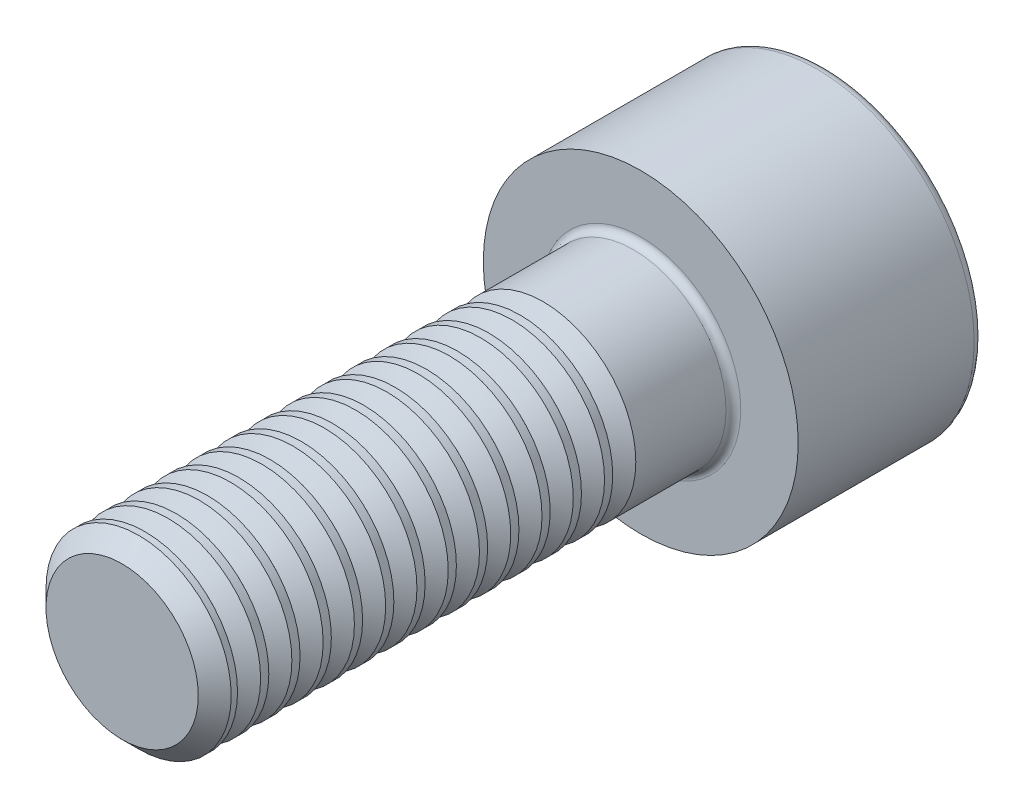
SolidWorks part; units mm, degrees
material "Acciaio inossidabile al cromo"
ref_plane "Piano frontale" through (0, 0, 0) normal (0, 0, 1) x (1, 0, 0)
ref_plane "Piano superiore" through (0, 0, 0) normal (0, 1, 0) x (1, 0, 0)
ref_plane "Piano destro" through (0, 0, 0) normal (1, 0, 0) x (0, 0, -1)
sketch "Schizzo1" plane through (0, 0, 0) normal (0, 0, 1) x (1, 0, 0)
  circle A0 centre (0, 0) radius 4.25
  dimension "D1" = 8.5
extrude "Estrusione-Estrusione1" add sketch "Schizzo1" along normal blind 5
sketch "Schizzo2" plane through (0, 0, 5) normal (0, 0, 1) x (1, 0, 0)
  circle A0 centre (0, 0) radius 2.5
  dimension "D1" = 5
extrude "Estrusione-Estrusione2" add sketch "Schizzo2" along normal blind 14
sketch "Schizzo3" plane through (0, 0, 0) normal (0, 0, -1) x (-1, 0, 0)
  line L1 (0, 2.358) -> (-2.0421, 1.179)
  line L2 (-2.0421, 1.179) -> (-2.0421, -1.179)
  line L3 (-2.0421, -1.179) -> (0, -2.358)
  line L4 (0, -2.358) -> (2.0421, -1.179)
  line L5 (2.0421, -1.179) -> (2.0421, 1.179)
  line L6 (2.0421, 1.179) -> (0, 2.358)
  circle A0 centre (0, 0) radius 2.0421 construction
  point P1 (0, 0)
  dimension "D1" = 2.358
extrude "Taglio-Estrusione1" cut sketch "Schizzo3" against normal blind 2.5
fillet "Raccordo1" radius 0.25 1 edges at (4.25, 0, 0)
fillet "Raccordo2" radius 0.2 1 edges at (2.5, 0, 5)
chamfer "Smusso1" distance 0.445 angle 45 1 edges at (2.5, 0, 19)
sketch "Schizzo4" plane through (0, 0, 0) normal (1, 0, 0) x (0, 0, -1)
  line L0 (-7.9451, -2.055) -> (-8.2567, -2.5)
  line L1 (-7.9451, -2.055) -> (-7.6335, -2.5)
  line L2 (-7.6335, -2.5) -> (-7.6335, -3.125)
  line L3 (-7.6335, -3.125) -> (-8.2567, -3.125)
  line L4 (-8.2567, -3.125) -> (-8.2567, -2.5)
  line L7 (-18.555, -2.5) -> (-5.2, -2.5) construction
  line L9 (0, -4) -> (0, 4) construction
  line L10 (0, 0) -> (-19, 0) construction
  line L11 (-19, 2.055) -> (-19, -2.055) construction
  dimension "D1" = 1.07
  dimension "D2" = 0.6232
  dimension "D3" = 0.625
  dimension "D4" = 0.3116
  dimension "D5" = 7.9451
revolve "Taglia-Rivoluzione1" cut sketch "Schizzo4" angle 360 about L10
pattern_linear "Ripetizione a L1" count 13 spacing 0.844 along (0, 0, 1) of "Taglia-Rivoluzione1"
sketch "Schizzo5" plane through (0, 0, 0) normal (1, 0, 0) x (0, 0, -1)
  line L0 (0, -2.042) -> (-2.5, -2.042)
  line L1 (-2.5, -2.042) -> (-3.6789, 0)
  line L2 (-3.6789, 0) -> (0, 0)
  line L3 (0, 0) -> (0, -2.042)
  point P4 (0, 0)
  dimension "D1" = 3.6789
  dimension "D2" = 2.042
  dimension "D3" = 2.5
revolve "Taglia-Rivoluzione2" cut sketch "Schizzo5" angle 360 about L2
